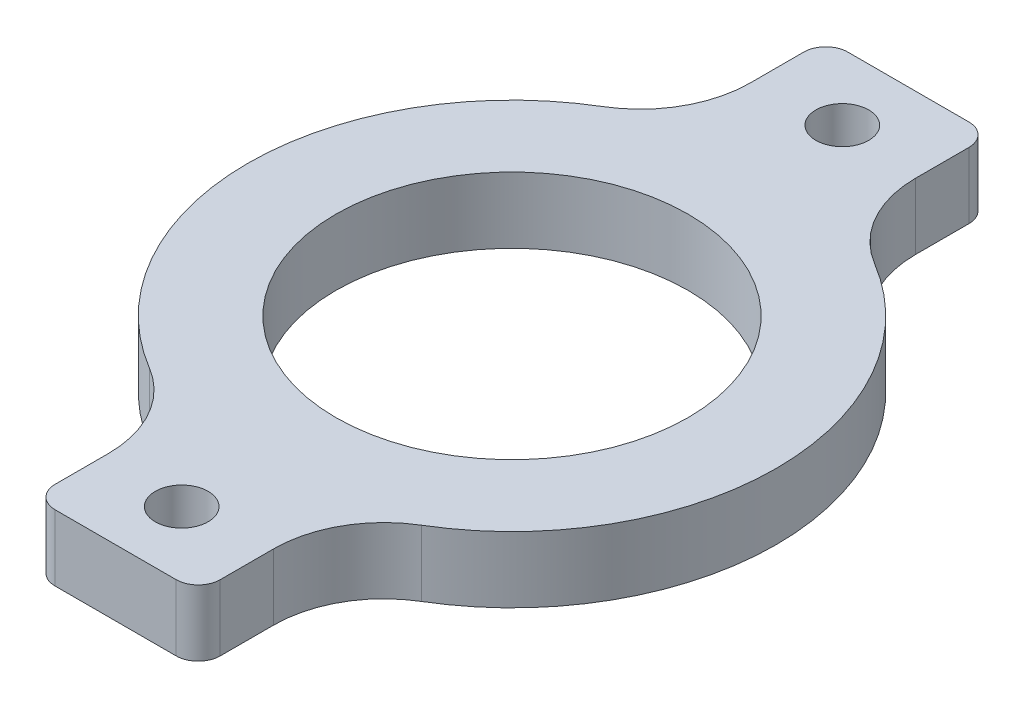
SolidWorks part; units mm, degrees
material "ABS PC"
ref_plane "Front Plane" through (0, 0, 0) normal (0, 0, 1) x (1, 0, 0)
ref_plane "Top Plane" through (0, 0, 0) normal (0, 1, 0) x (1, 0, 0)
ref_plane "Right Plane" through (0, 0, 0) normal (1, 0, 0) x (0, 0, -1)
sketch "Sketch1" plane through (0, 0, 0) normal (0, 1, 0) x (1, 0, 0)
  line L0 (0, 0) -> (0, 18) construction
  line L1 (-3.75, 18) -> (3.75, 18)
  line L2 (3.75, 18) -> (3.75, 11.399)
  line L3 (-3.75, 18) -> (-3.75, 11.399)
  line L4 (0, 0) -> (6.7263, 0) construction
  line L5 (-3.75, -18) -> (-3.75, -11.399)
  line L6 (-3.75, -18) -> (3.75, -18)
  line L7 (3.75, -18) -> (3.75, -11.399)
  circle A0 centre (0, 0) radius 8
  arc A1 (-3.75, 11.399) -> (-3.75, -11.399) centre (0, 0) ccw
  arc A2 (3.75, -11.399) -> (3.75, 11.399) centre (0, 0) ccw
  point P3 (0, -12)
  point P9 (0, 12)
  dimension "D1" = 16
  dimension "D2" = 24
  dimension "D3" = 7.5
  dimension "D4" = 6
extrude "Boss-Extrude1" add sketch "Sketch1" along normal blind 3
sketch "Sketch2" plane through (0, 3, 0) normal (0, 1, 0) x (1, 0, 0)
  line L0 (0, 0) -> (5.2599, 0) construction
  line L1 (0, 0) -> (0, 18) construction
  line L2 (3.75, 18) -> (-3.75, 18) construction
  point P3 (0, 15)
  point P7 (0, -15)
  dimension "D1" = 30
hole_wizard "M2 Clearance Hole1" positions "Sketch2" profile "Sketch3" hole size "M2" standard "ANSI Metric" end condition through all
sketch "Sketch3" plane through (0, 3, 15) normal (1, 0, 0) x (0, 0, 1)
  line L0 (0, 0) -> (0, 3)
  line L1 (0, 3) -> (1.2, 3)
  line L2 (1.2, 3) -> (1.2, 0)
  line L5 (1.2, 0) -> (0, 0)
  line L11 (0, -6.35) -> (0, 107.95) construction
  dimension "Thru Hole Dia." = 2.4
  dimension "Thru Hole Depth" = 3
fillet "Fillet1" radius 5 4 edges at (-3.75, 1.5, 11.399) (3.75, 1.5, 11.399) (3.75, 1.5, -11.399) (-3.75, 1.5, -11.399)
fillet "Fillet2" radius 1 4 edges at (3.75, 1.5, 18) (-3.75, 1.5, 18) (3.75, 1.5, -18) (-3.75, 1.5, -18)
